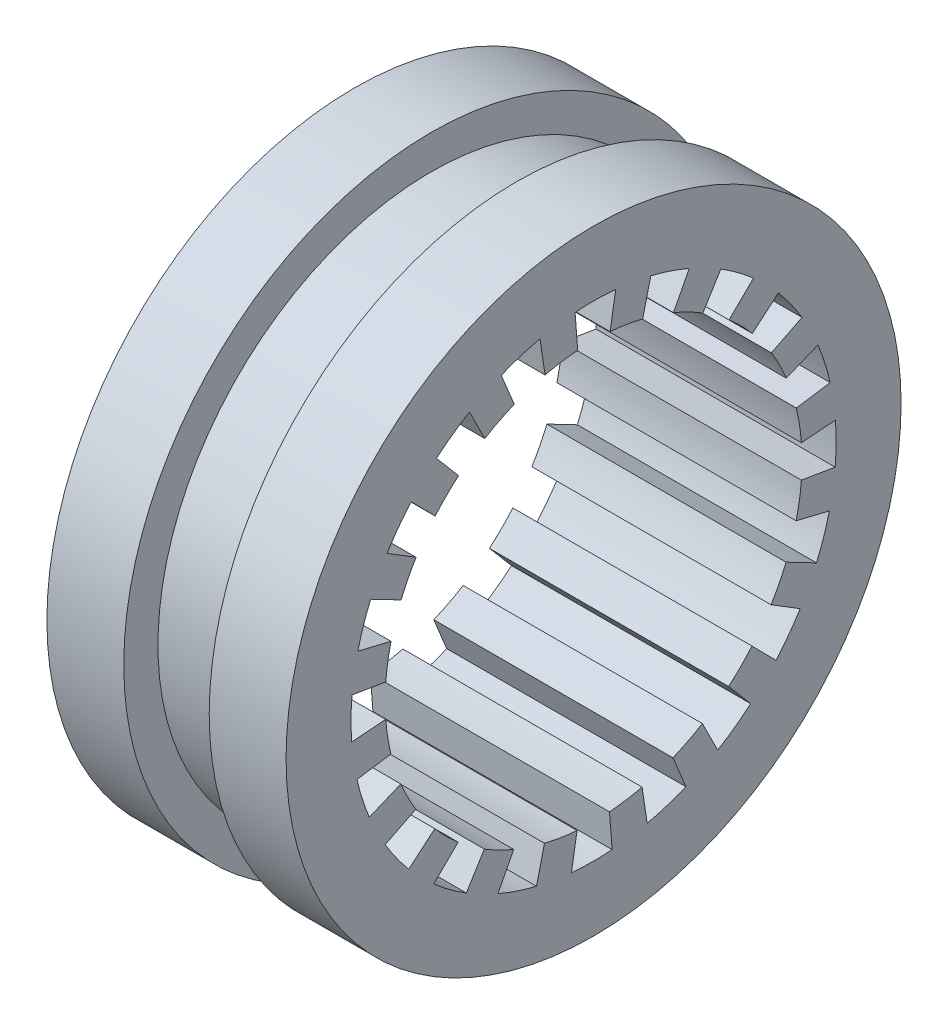
SolidWorks part; units mm, degrees
ref_plane "Front Plane" through (0, 0, 0) normal (0, 0, 1) x (1, 0, 0)
ref_plane "Top Plane" through (0, 0, 0) normal (0, 1, 0) x (1, 0, 0)
ref_plane "Right Plane" through (0, 0, 0) normal (1, 0, 0) x (0, 0, -1)
sketch "Sketch1" plane through (0, 0, 0) normal (1, 0, 0) x (0, 0, -1)
  circle A0 centre (0, 0) radius 61
  circle A1 centre (0, 0) radius 72.5 construction
  circle A2 centre (0, 0) radius 90
  dimension "D1" = 122
  dimension "D2" = 145
  dimension "D3" = 180
extrude "Boss-Extrude1" add sketch "Sketch1" along normal mid plane 70
sketch "Sketch2" plane through (35, 0, 0) normal (1, 0, 0) x (0, 0, -1)
  line L0 (0, 0) -> (0, 105.2885) construction
  line L1 (0, 51.3958) -> (-4.5, 58.8281)
  line L2 (0, 51.3958) -> (4.5, 58.8281)
  line L3 (-4.5, 58.8281) -> (-5.4153, 70.7932)
  line L4 (4.5, 58.8281) -> (6.482, 70.7035)
  circle A0 centre (0, 0) radius 59
  circle A1 centre (0, 0) radius 71 construction
  arc A2 (-5.4153, 70.7932) -> (6.482, 70.7035) centre (0, 0) cw
  circle M3 centre (0, 0) radius 61
  dimension "D1" = 142
  dimension "D3" = 118
  dimension "D2" = 4.5
extrude "Cut-Extrude1" cut sketch "Sketch2" against normal through all contours A2 L3 A0 L4 | L1 L2 M3
pattern_circular "CirPattern1" count 20 over 360 about axis through (0, 0, 0) along (1, 0, 0) of "Cut-Extrude1"
sketch "Sketch3" plane through (35, 0, 0) normal (1, 0, 0) x (0, 0, -1)
  circle A0 centre (0, 0) radius 80
  circle A1 centre (0, 0) radius 90
  dimension "D1" = 180
  dimension "D2" = 160
extrude "Cut-Extrude2" cut sketch "Sketch3" against normal mid plane 25 from offset 35
